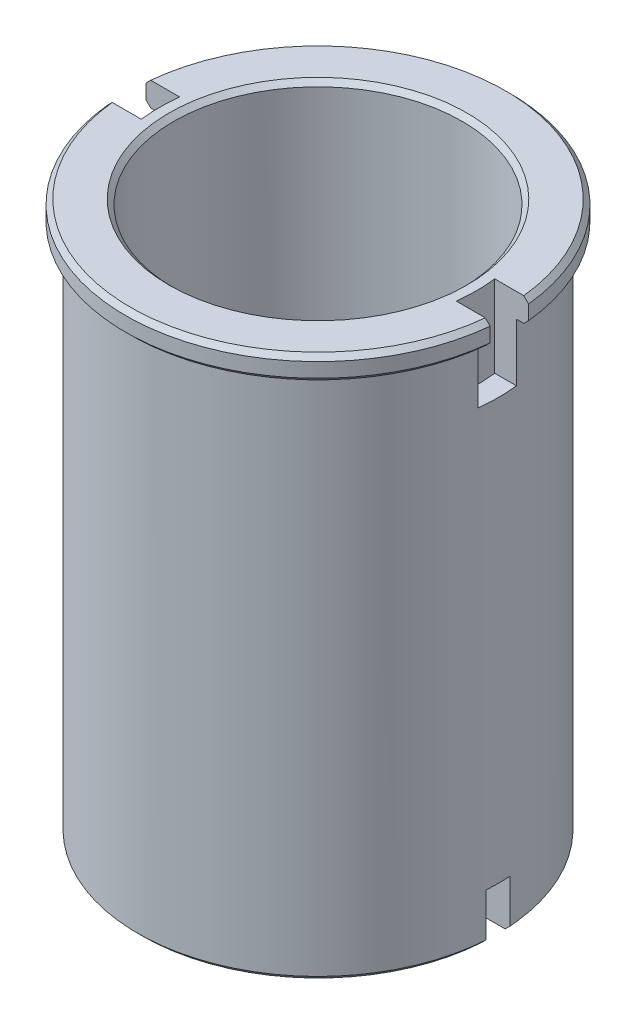
SolidWorks part; units mm, degrees
material "PA Type 6"
ref_plane "Front Plane" through (0, 0, 0) normal (0, 0, 1) x (1, 0, 0)
ref_plane "Top Plane" through (0, 0, 0) normal (0, 1, 0) x (1, 0, 0)
ref_plane "Right Plane" through (0, 0, 0) normal (1, 0, 0) x (0, 0, -1)
sketch "Sketch1" plane through (0, 0, 0) normal (0, 1, 0) x (1, 0, 0)
  circle A0 centre (0, 0) radius 37.5
  circle A2 centre (0, 0) radius 30
  dimension "D1" = 75
  dimension "D2" = 60
extrude "Boss-Extrude1" add sketch "Sketch1" along normal mid plane 114.5
sketch "Sketch2" plane through (0, 57.25, 0) normal (0, 1, 0) x (1, 0, 0)
  circle A0 centre (0, 0) radius 40
  circle A1 centre (0, 0) radius 37.5 construction
  circle A2 centre (0, 0) radius 37.5
  dimension "D1" = 80
extrude "Boss-Extrude2" add sketch "Sketch2" against normal blind 5
sketch "Sketch3" plane through (0, -57.25, 0) normal (0, -1, 0) x (1, 0, 0)
  line L1 (-45, 2.5) -> (45, 2.5)
  line L2 (-45, 2.5) -> (-45, -2.5)
  line L3 (-45, -2.5) -> (45, -2.5)
  line L4 (45, 2.5) -> (45, -2.5)
  line L5 (-45, 2.5) -> (45, -2.5) construction
  line L6 (-45, -2.5) -> (45, 2.5) construction
  point P0 (0, 0)
  dimension "D1" = 5
  dimension "D2" = 90
extrude "Cut-Extrude1" cut sketch "Sketch3" against normal blind 10
sketch "Sketch4" plane through (0, 57.25, 0) normal (0, 1, 0) x (1, 0, 0)
  line L1 (50, -4) -> (-50, -4)
  line L2 (50, -4) -> (50, 4)
  line L3 (50, 4) -> (-50, 4)
  line L4 (-50, -4) -> (-50, 4)
  line L5 (50, -4) -> (-50, 4) construction
  line L6 (50, 4) -> (-50, -4) construction
  circle A0 centre (0, 0) radius 33
  circle A1 centre (0, 0) radius 30 construction
  point P0 (0, 0)
  circle M6 centre (0, 0) radius 40
  dimension "D3" = 3
  dimension "D1" = 8
  dimension "D2" = 100
extrude "Cut-Extrude2" cut sketch "Sketch4" against normal blind 17 contours A0 L1 L3 M6 | A0 L3 L1 M6
chamfer "Chamfer1" distance 1 angle 45 9 edges at (0, 52.25, -40) (0, 57.25, -40) (0, 52.25, 40) (0, 57.25, 40) (0, -57.25, 37.5) (0, -57.25, -37.5) (0, -57.25, -30) (0, -57.25, 30) (0, 57.25, 30)
